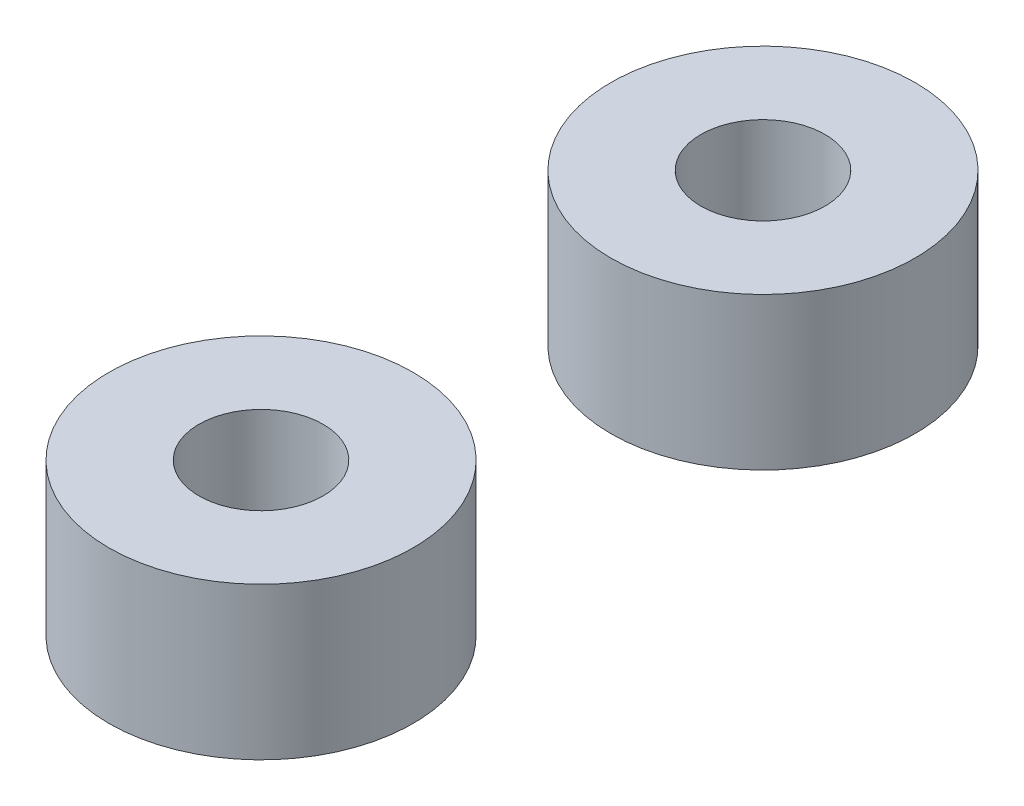
SolidWorks part; units mm, degrees
ref_plane "前视基准面" through (0, 0, 0) normal (0, 0, 1) x (1, 0, 0)
ref_plane "上视基准面" through (0, 0, 0) normal (0, 1, 0) x (1, 0, 0)
ref_plane "右视基准面" through (0, 0, 0) normal (1, 0, 0) x (0, 0, -1)
sketch "草图1" plane through (0, 0, 0) normal (0, 1, 0) x (1, 0, 0)
  line L0 (0, 6.7437) -> (0, -6.8111) construction
  line L1 (-4.5216, 0) -> (7.8641, 0) construction
  circle A0 centre (0, 4.9501) radius 1.05
  circle A1 centre (0, 4.9501) radius 3
  circle A2 centre (0, -4.9501) radius 3
  circle A3 centre (0, -4.9501) radius 1.05
  circle A4 centre (10, -4.9501) radius 3
  circle A5 centre (10, 4.9501) radius 1.075
  circle A6 centre (20, 4.9501) radius 1.225
  circle A7 centre (10, 4.9501) radius 3
  circle A8 centre (20, -4.9501) radius 3
  circle A9 centre (30, 4.9501) radius 1.125
  circle A10 centre (30, -4.9501) radius 1.125
  circle A11 centre (20, 4.9501) radius 3
  circle A12 centre (30, -4.9501) radius 3
  circle A13 centre (20, -4.9501) radius 1.225
  circle A14 centre (10, -4.9501) radius 1.075
  circle A15 centre (30, 4.9501) radius 3
  circle A16 centre (10, 4.9501) radius 1.05 [skipped]
  circle A17 centre (20, 4.9501) radius 1.05 [skipped]
  circle A18 centre (30, 4.9501) radius 1.05 [skipped]
  circle A19 centre (30, -4.9501) radius 1.05 [skipped]
  circle A20 centre (20, -4.9501) radius 1.05 [skipped]
  circle A21 centre (10, -4.9501) radius 1.05 [skipped]
  dimension "D1" = 2.1
  dimension "D2" = 6
  dimension "D4" = 2.15
  dimension "D5" = 2.45
  dimension "D6" = 2.25
  dimension "D3" = 4
extrude "凸台-拉伸1" add sketch "草图1" along normal blind 3
sketch "草图2" plane through (0, 0, 0) normal (0, 1, 0) x (1, 0, 0)
  line L1 (-6.6781, 11.2845) -> (15.3712, 11.2845)
  line L2 (-6.6781, 11.2845) -> (-6.6781, -15.2934)
  line L3 (-6.6781, -15.2934) -> (15.3712, -15.2934)
  line L4 (15.3712, 11.2845) -> (15.3712, -15.2934)
  line L5 (25.2451, 13.0662) -> (40.7613, 13.0662)
  line L6 (25.2451, 13.0662) -> (25.2451, -14.4026)
  line L7 (25.2451, -14.4026) -> (40.7613, -14.4026)
  line L8 (40.7613, 13.0662) -> (40.7613, -14.4026)
extrude "切除-拉伸3" cut sketch "草图2" along normal through all
